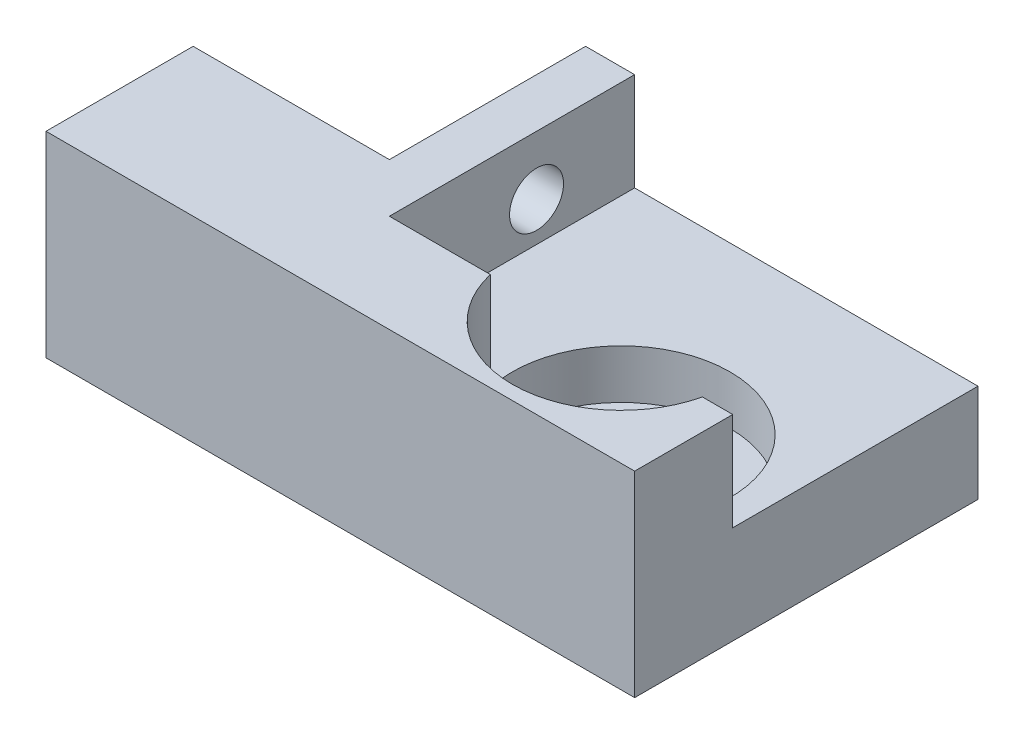
SolidWorks part; units mm, degrees
ref_plane "Front Plane" through (0, 0, 0) normal (0, 0, 1) x (1, 0, 0)
ref_plane "Top Plane" through (0, 0, 0) normal (0, 1, 0) x (1, 0, 0)
ref_plane "Right Plane" through (0, 0, 0) normal (1, 0, 0) x (0, 0, -1)
sketch "Sketch1" plane through (0, 0, 0) normal (0, 1, 0) x (1, 0, 0)
  line L1 (0, 0) -> (60, 0)
  line L2 (0, 0) -> (0, 15)
  line L3 (20, 35) -> (60, 35)
  line L4 (60, 0) -> (60, 35)
  line L7 (0, 15) -> (20, 15)
  line L8 (20, 35) -> (20, 15)
  dimension "D1" = 15
  dimension "D2" = 60
extrude "Boss-Extrude1" add sketch "Sketch1" along normal blind 20
sketch "Sketch2" plane through (0, 20, 0) normal (0, 1, 0) x (1, 0, 0)
  line L0 (20, 35) -> (20, 15) construction
  line L1 (60, 35) -> (25, 35)
  line L2 (60, 35) -> (60, 10)
  line L3 (60, 10) -> (25, 10)
  line L4 (25, 35) -> (25, 10)
  dimension "D1" = 25
  dimension "D2" = 5
extrude "Cut-Extrude1" cut sketch "Sketch2" against normal blind 10
sketch "Sketch3" plane through (0, 10, 0) normal (0, 1, 0) x (1, 0, 0)
  line L0 (25, 35) -> (25, 10) construction
  circle A0 centre (46.1, 12.5258) radius 11.1
  dimension "D1" = 22.2
  dimension "D2" = 10
extrude "Cut-Extrude2" cut sketch "Sketch3" against normal blind 25 from offset 20
sketch "Sketch4" plane through (0, 5, 0) normal (0, 1, 0) x (1, 0, 0)
  circle A0 centre (46.1, 12.5258) radius 5
  dimension "D1" = 10
extrude "Cut-Extrude3" cut sketch "Sketch4" against normal through all
sketch "Sketch5" plane through (25, 0, 0) normal (1, 0, 0) x (0, 0, -1)
  line L0 (35, 20) -> (10, 20) construction
  line L2 (15, 20) -> (15, 0) construction
  circle A0 centre (25, 14) radius 2.75
  point P4 (22.5, 20)
  dimension "D1" = 5.5
  dimension "D2" = 6
  dimension "D3" = 10
extrude "Cut-Extrude4" cut sketch "Sketch5" against normal through all
